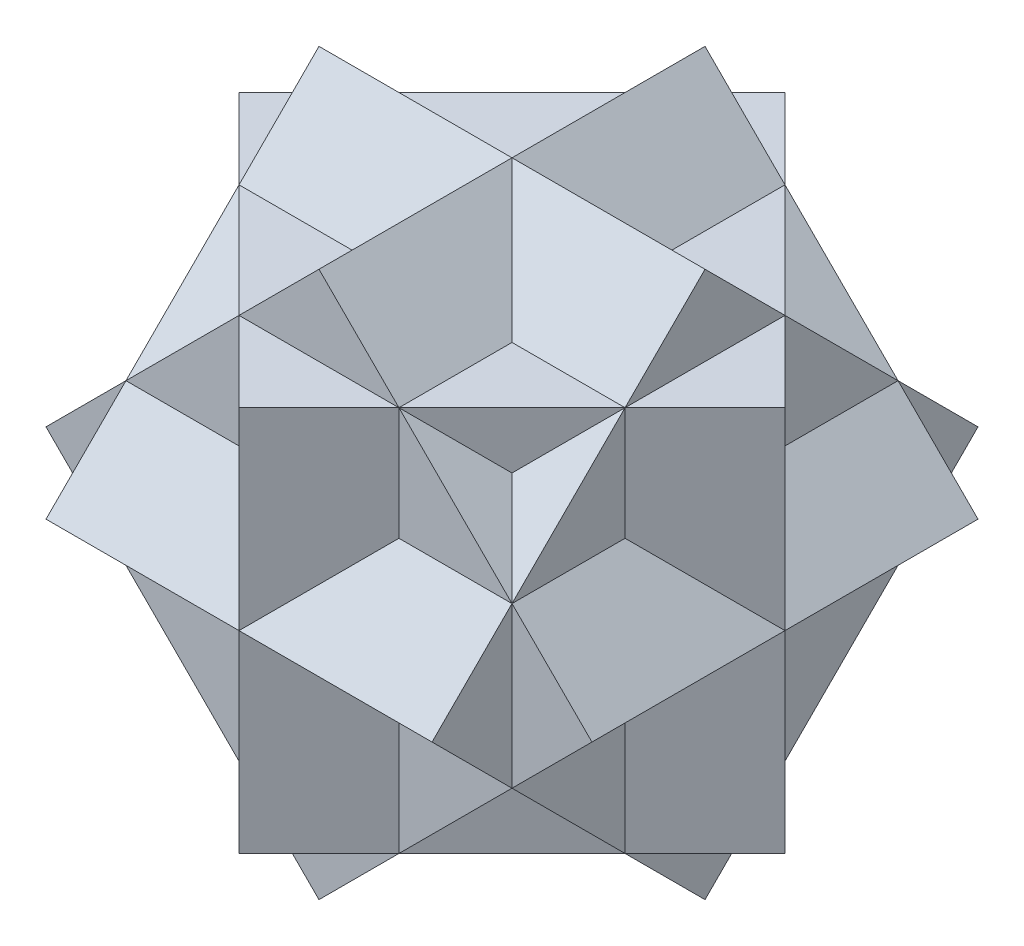
SolidWorks part; units mm, degrees
ref_plane "Front Plane" through (0, 0, 0) normal (0, 0, 1) x (1, 0, 0)
ref_plane "Top Plane" through (0, 0, 0) normal (0, 1, 0) x (1, 0, 0)
ref_plane "Right Plane" through (0, 0, 0) normal (1, 0, 0) x (0, 0, -1)
sketch "Sketch3" plane through (0, 0, 0) normal (0, 0, 1) x (1, 0, 0)
  line L0 (-153.0248, 0) -> (0, 153.0248)
  line L1 (-153.0248, 0) -> (0, -153.0248)
  line L2 (0, 153.0248) -> (153.0248, 0)
  line L3 (0, -153.0248) -> (153.0248, 0)
  line L4 (-153.0248, 0) -> (153.0248, 0) construction
  line L5 (0, 153.0248) -> (0, -153.0248) construction
  point P1 (0, 0)
  dimension "D1" = 216.4098
sketch "Sketch4" plane through (0, 0, 0) normal (0, 1, 0) x (1, 0, 0)
  line L0 (-153.0248, 0) -> (0, 153.0248)
  line L1 (-153.0248, 0) -> (0, -153.0248)
  line L2 (0, 153.0248) -> (153.0248, 0)
  line L3 (0, -153.0248) -> (153.0248, 0)
  line L4 (-153.0248, 0) -> (153.0248, 0) construction
  line L5 (0, 153.0248) -> (0, -153.0248) construction
  point P1 (0, 0)
sketch "Sketch5" plane through (0, 0, 0) normal (1, 0, 0) x (0, 0, -1)
  line L0 (-153.0248, 0) -> (0, 153.0248)
  line L1 (-153.0248, 0) -> (0, -153.0248)
  line L2 (0, 153.0248) -> (153.0248, 0)
  line L3 (0, -153.0248) -> (153.0248, 0)
  line L4 (-153.0248, 0) -> (153.0248, 0) construction
  line L5 (0, 153.0248) -> (0, -153.0248) construction
  line L6 (0, 153.0248) -> (0, -153.0248) construction
  point P1 (0, 0)
extrude "Boss-Extrude1" add sketch "Sketch3" along normal mid plane 216.4098
extrude "Boss-Extrude2" add sketch "Sketch4" along normal mid plane 216.4098
extrude "Boss-Extrude3" add sketch "Sketch5" along normal mid plane 216.4098
equation "\"side_length\"= 4 * 2.238285 - 2 * \"Subtract\""
equation "\"D1@Sketch3\"=\"side_length\""
equation "\"D1@Boss-Extrude1\"=\"side_length\""
equation "\"D1@Boss-Extrude2\"=\"side_length\""
equation "\"D1@Boss-Extrude3\"=\"side_length\""
equation "\"Joiner_spacing\"= 0.1"
equation "\"Subtract\"= 5.5mm"
